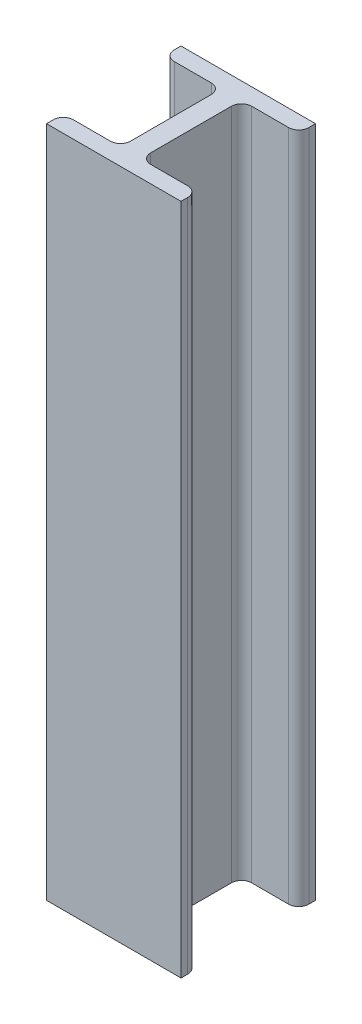
SolidWorks part; units mm, degrees
ref_plane "Front Plane" through (0, 0, 0) normal (0, 0, 1) x (1, 0, 0)
ref_plane "Top Plane" through (0, 0, 0) normal (0, 1, 0) x (1, 0, 0)
ref_plane "Right Plane" through (0, 0, 0) normal (1, 0, 0) x (0, 0, -1)
sketch "Sketch1" plane through (0, 0, 0) normal (0, 1, 0) x (1, 0, 0)
  line L0 (-20, 0) -> (20, 0)
  line L1 (20, 0) -> (20, 5)
  line L2 (20, 5) -> (3, 5)
  line L3 (3, 5) -> (3, 35)
  line L6 (3, 35) -> (20, 35)
  line L7 (20, 35) -> (20, 40)
  line L8 (20, 40) -> (-20, 40)
  line L9 (0, 40) -> (0, 0)
  line L10 (-20, 35) -> (-20, 40)
  line L11 (-3, 35) -> (-20, 35)
  line L12 (-3, 5) -> (-3, 35)
  line L13 (-20, 5) -> (-3, 5)
  line L14 (-20, 0) -> (-20, 5)
  dimension "D1" = 40
  dimension "D2" = 5
  dimension "D3" = 5
  dimension "D4" = 3
  dimension "D5" = 20
  dimension "D6" = 20
extrude "Boss-Extrude1" add sketch "Sketch1" along normal blind 200 contours L14 L0 L9 L8 L10 L11 L12 L13 | L8 L9 L0 L1 L2 L3 L6 L7
fillet "Fillet1" radius 3 4 edges at (-3, 100, -5) (-3, 100, -35) (3, 100, -35) (3, 100, -5)
fillet "Fillet2" radius 3 4 edges at (20, 100, -5) (-20, 100, -5) (-20, 100, -35) (20, 100, -35)
